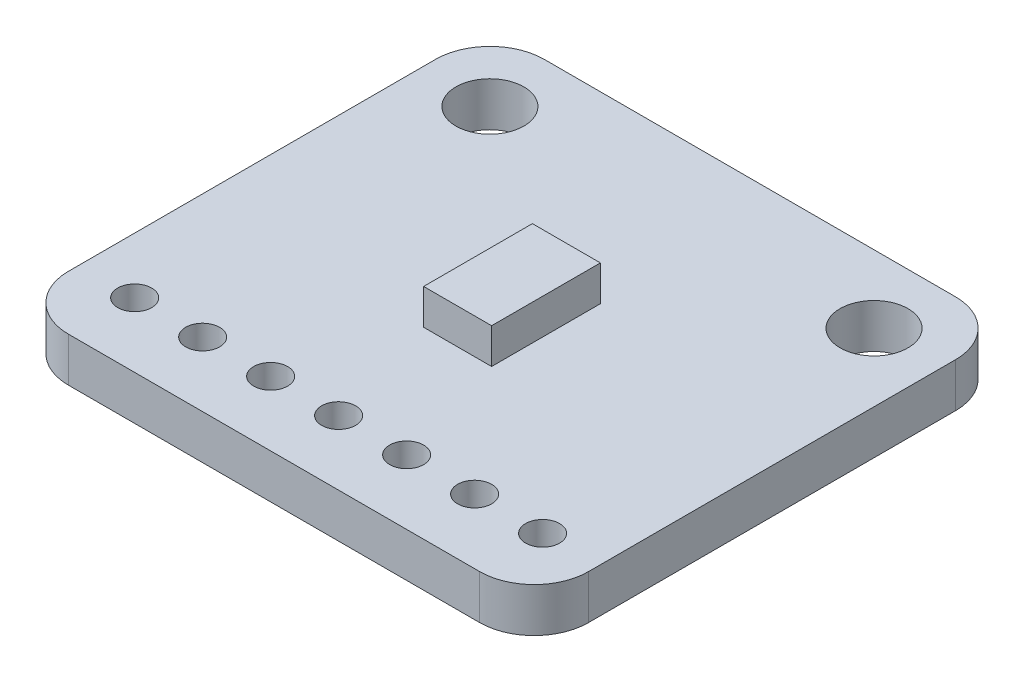
SolidWorks part; units mm, degrees
ref_plane "Front Plane" through (0, 0, 0) normal (0, 0, 1) x (1, 0, 0)
ref_plane "Top Plane" through (0, 0, 0) normal (0, 1, 0) x (1, 0, 0)
ref_plane "Right Plane" through (0, 0, 0) normal (1, 0, 0) x (0, 0, -1)
sketch "Sketch1" plane through (0, 0, 0) normal (0, 1, 0) x (1, 0, 0)
  line L0 (0, 2.413) -> (19.431, 2.413) construction
  line L1 (2.032, 0) -> (17.399, 0)
  line L2 (0, 2.032) -> (0, 15.748)
  line L3 (2.032, 17.78) -> (17.399, 17.78)
  line L4 (19.431, 2.032) -> (19.431, 15.748)
  circle A0 centre (2.54, 15.24) radius 1.27
  circle A1 centre (16.891, 15.24) radius 1.27
  circle A2 centre (2.0955, 2.413) radius 0.635
  circle A3 centre (4.6355, 2.413) radius 0.635
  circle A4 centre (7.1755, 2.413) radius 0.635
  circle A5 centre (9.7155, 2.413) radius 0.635
  circle A6 centre (12.2555, 2.413) radius 0.635
  circle A7 centre (14.7955, 2.413) radius 0.635
  circle A8 centre (17.3355, 2.413) radius 0.635
  arc A9 (2.032, 0) -> (0, 2.032) centre (2.032, 2.032) cw
  arc A10 (17.399, 0) -> (19.431, 2.032) centre (17.399, 2.032) ccw
  arc A11 (19.431, 15.748) -> (17.399, 17.78) centre (17.399, 15.748) ccw
  arc A12 (0, 15.748) -> (2.032, 17.78) centre (2.032, 15.748) cw
  point P25 (12.377, 2.413)
  point P26 (22.6929, 2.413)
  point P29 (0, 0)
  point P32 (19.431, 0)
  point P37 (0, 17.78)
  dimension "D3" = 1.27
  dimension "D4" = 1.27
  dimension "D5" = 1.27
  dimension "D6" = 1.27
  dimension "D7" = 1.27
  dimension "D8" = 1.27
  dimension "D9" = 1.27
  dimension "D10" = 2.54
  dimension "D11" = 2.54
  dimension "D15" = 2.54
  dimension "D16" = 2.54
  dimension "D17" = 2.413
  dimension "D18" = 2.54
  dimension "D19" = 2.54
  dimension "D20" = 2.54
  dimension "D21" = 2.54
  dimension "D22" = 2.54
  dimension "D23" = 2.032
  dimension "D1" = 17.78
  dimension "D2" = 19.431
  dimension "D12" = 2.54
  dimension "D13" = 2.54
  dimension "D14" = 2.54
extrude "Boss-Extrude1" add sketch "Sketch1" along normal blind 1.651
sketch "Sketch2" plane through (0, 1.651, 0) normal (0, 1, 0) x (1, 0, 0)
  line L0 (0.5952, 17.1848) -> (18.8358, 0.5952) construction
  line L2 (9.7155, 8.89) -> (8.4455, 8.89)
  line L3 (9.7155, 8.89) -> (9.7155, 6.858)
  line L4 (9.7155, 6.858) -> (8.4455, 6.858)
  line L5 (8.4455, 8.89) -> (8.4455, 6.858)
  line L6 (8.4455, 6.858) -> (10.9855, 6.858)
  line L7 (8.4455, 6.858) -> (8.4455, 10.922)
  line L8 (8.4455, 10.922) -> (10.9855, 10.922)
  line L9 (10.9855, 6.858) -> (10.9855, 10.922)
  arc A0 (2.032, 17.78) -> (0, 15.748) centre (2.032, 15.748) ccw construction
  arc A1 (17.399, 0) -> (19.431, 2.032) centre (17.399, 2.032) ccw construction
  dimension "D1" = 2.032
  dimension "D2" = 4.064
  dimension "D3" = 1.27
  dimension "D4" = 2.54
extrude "Boss-Extrude2" add sketch "Sketch2" along normal blind 1.3208 contours L2 L5 L4 L3 | L7 L0 L9 L8 | L0 L3 L6 L9 | L0 L7 L2
